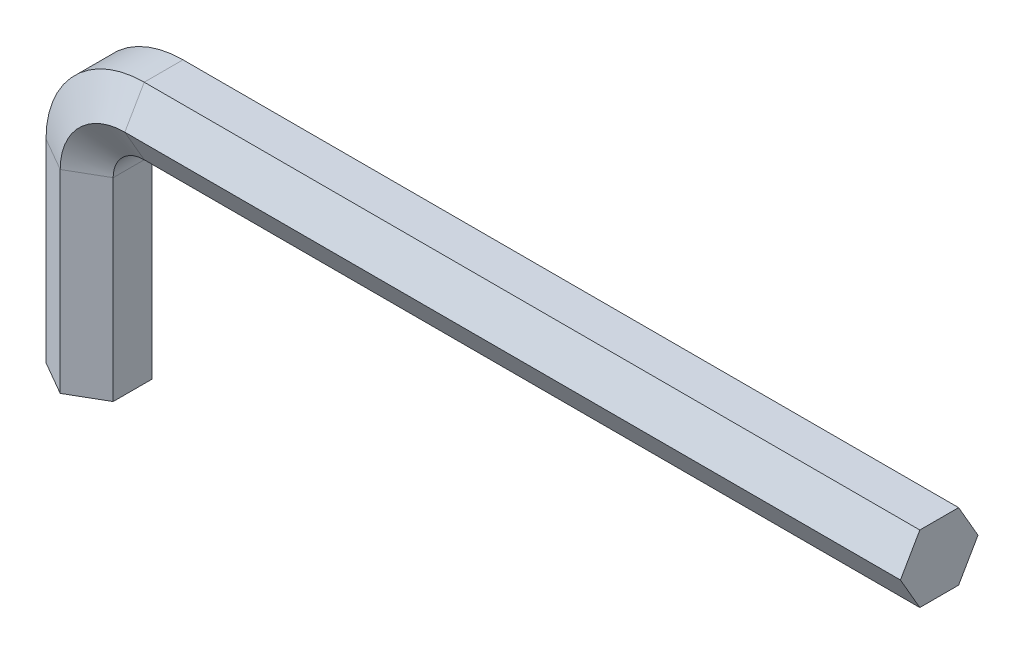
SolidWorks part; units mm, degrees
ref_plane "Front Plane" through (0, 0, 0) normal (0, 0, 1) x (1, 0, 0)
ref_plane "Top Plane" through (0, 0, 0) normal (0, 1, 0) x (1, 0, 0)
ref_plane "Right Plane" through (0, 0, 0) normal (1, 0, 0) x (0, 0, -1)
sketch "Sketch1" plane through (0, 0, 0) normal (0, 0, 1) x (1, 0, 0)
  line L0 (0, 0) -> (0, 15)
  line L1 (5, 20) -> (65, 20)
  arc A0 (0, 15) -> (5, 20) centre (5, 15) cw
  dimension "D1" = 5
  dimension "D2" = 15
  dimension "D3" = 60
ref_plane "Plane1" through (65, 20, 0) normal (1, 0, 0) x (0, 0, -1)
sketch "Sketch2" plane through (65, 20, 0) normal (1, 0, 0) x (0, 0, -1)
  line L0 (0, 0) -> (0, -5) construction
  line L1 (3, 0) -> (1.5, 2.5981)
  line L2 (1.5, 2.5981) -> (-1.5, 2.5981)
  line L3 (-1.5, 2.5981) -> (-3, 0)
  line L4 (-3, 0) -> (-1.5, -2.5981)
  line L5 (-1.5, -2.5981) -> (1.5, -2.5981)
  line L6 (1.5, -2.5981) -> (3, 0)
  circle A0 centre (0, 0) radius 2.5981 construction
  dimension "D1" = 3
sweep "Sweep1" add profiles "Sketch2" path "Sketch1"
